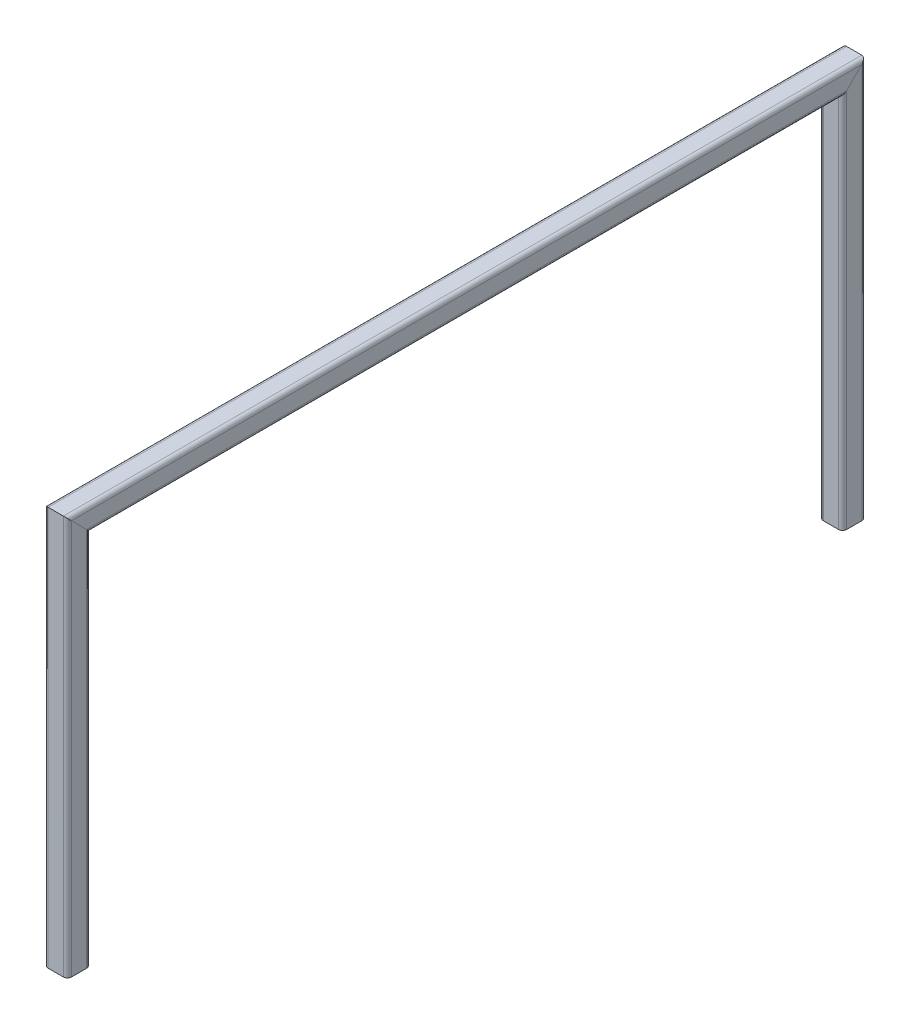
SolidWorks part; units mm, degrees
ref_plane "Front Plane" through (0, 0, 0) normal (0, 0, 1) x (1, 0, 0)
ref_plane "Top Plane" through (0, 0, 0) normal (0, 1, 0) x (1, 0, 0)
ref_plane "Right Plane" through (0, 0, 0) normal (1, 0, 0) x (0, 0, -1)
sketch "Sketch1" plane through (0, 0, 0) normal (1, 0, 0) x (0, 0, -1)
  line L1 (500, 250) -> (-500, 250)
  line L2 (500, 250) -> (500, -250)
  line L3 (500, -250) -> (-500, -250)
  line L4 (-500, 250) -> (-500, -250)
  line L5 (500, 250) -> (-500, -250) construction
  line L6 (500, -250) -> (-500, 250) construction
  point P0 (0, 0)
  dimension "D1" = 1000
  dimension "D2" = 500
other "Square tube 30 X 30 X 2.6(1)"
ref_plane "Plane1" through (0, 250, -500) normal (0, -1, 0) x (0, 0, -1)
sketch "Sketch18" plane through (0, 250, -500) normal (0, -1, 0) x (0, 0, -1)
  line L0 (-9.8, -12.4) -> (9.8, -12.4)
  line L1 (-12.4, -9.8) -> (-12.4, 9.8)
  line L2 (9.8, 12.4) -> (-9.8, 12.4)
  line L3 (12.4, 9.8) -> (12.4, -9.8)
  line L4 (-9.8, -15) -> (9.8, -15)
  line L5 (-15, -9.8) -> (-15, 9.8)
  line L6 (9.8, 15) -> (-9.8, 15)
  line L7 (15, 9.8) -> (15, -9.8)
  arc A0 (15, 9.8) -> (9.8, 15) centre (9.8, 9.8) ccw
  arc A1 (9.8, -15) -> (15, -9.8) centre (9.8, -9.8) ccw
  arc A2 (-15, -9.8) -> (-9.8, -15) centre (-9.8, -9.8) ccw
  arc A3 (-9.8, 15) -> (-15, 9.8) centre (-9.8, 9.8) ccw
  arc A4 (-9.8, 12.4) -> (-12.4, 9.8) centre (-9.8, 9.8) ccw
  arc A5 (12.4, 9.8) -> (9.8, 12.4) centre (9.8, 9.8) ccw
  arc A6 (9.8, -12.4) -> (12.4, -9.8) centre (9.8, -9.8) ccw
  arc A7 (-12.4, -9.8) -> (-9.8, -12.4) centre (-9.8, -9.8) ccw
  point P0 (-15, 0)
  point P1 (15, 0)
  point P2 (0, 15)
  point P3 (0, -15)
  point P4 (0, 0)
  point P5 (-15, -15)
  point P6 (15, -15)
  point P7 (15, 15)
  point P8 (-15, 15)
  point P33 (0, 0)
  dimension "D1" = 5.2
  dimension "Thickness" = 2.6
  dimension "V_leg" = 30
